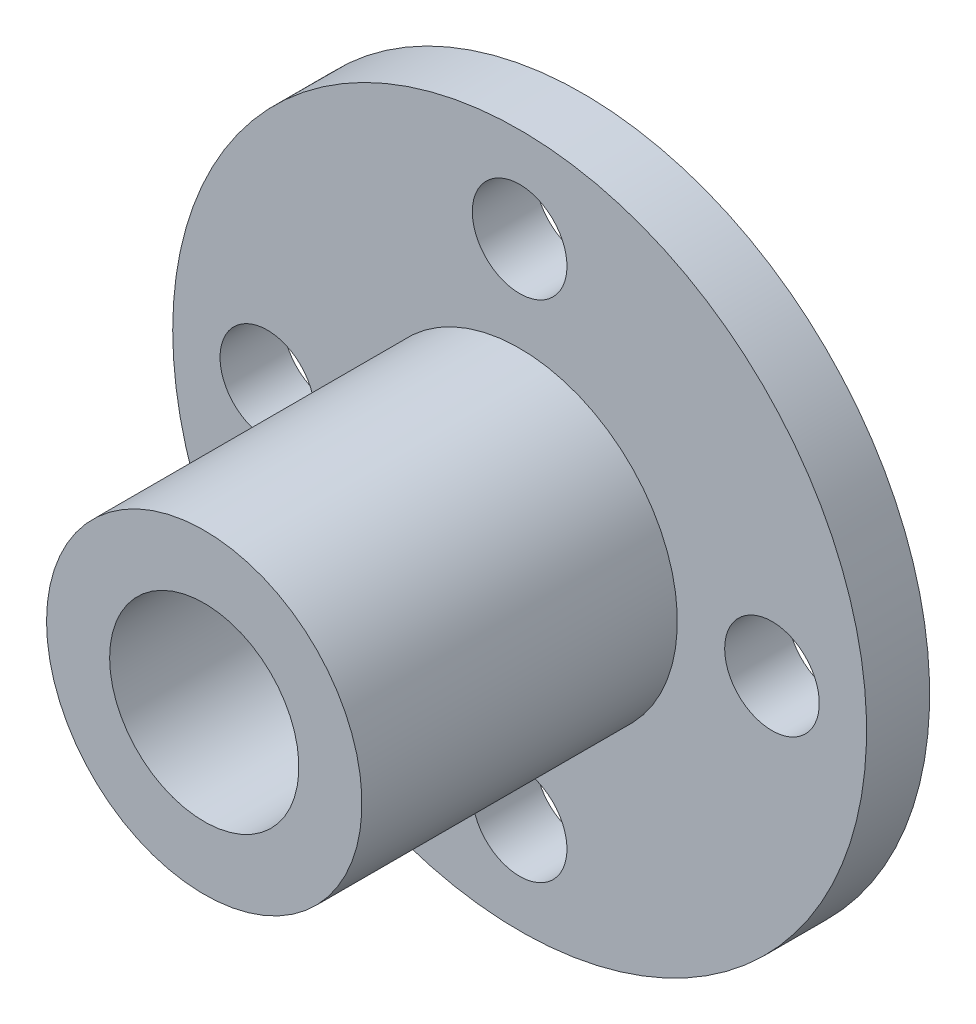
SolidWorks part; units mm, degrees
ref_plane "前视基准面" through (0, 0, 0) normal (0, 0, 1) x (1, 0, 0)
ref_plane "上视基准面" through (0, 0, 0) normal (0, 1, 0) x (1, 0, 0)
ref_plane "右视基准面" through (0, 0, 0) normal (1, 0, 0) x (0, 0, -1)
other "Configuration Table"
sketch "草图1" plane through (0, 0, 0) normal (0, 1, 0) x (1, 0, 0)
  line L0 (0, 0) -> (5, 0)
  line L1 (5, 0) -> (5, 10)
  line L2 (5, 10) -> (11, 10)
  line L3 (11, 10) -> (11, 12)
  line L4 (11, 12) -> (0, 12)
  line L5 (0, 12) -> (0, 0)
revolve "旋转1" add sketch "草图1" angle 360 about L5
sketch "草图2" plane through (0, 0, -12) normal (0, 0, -1) x (-1, 0, 0)
  line L0 (0, 0) -> (8, 0)
  circle A0 centre (8, 0) radius 1.5
  circle A1 centre (0, -8) radius 1.5
  circle A2 centre (-8, 0) radius 1.5
  circle A3 centre (0, 8) radius 1.5
  circle A4 centre (0, 0) radius 3
  point P14 (0, 0)
  dimension "D1" = 4
extrude "切除-拉伸1" cut sketch "草图2" against normal blind 25
